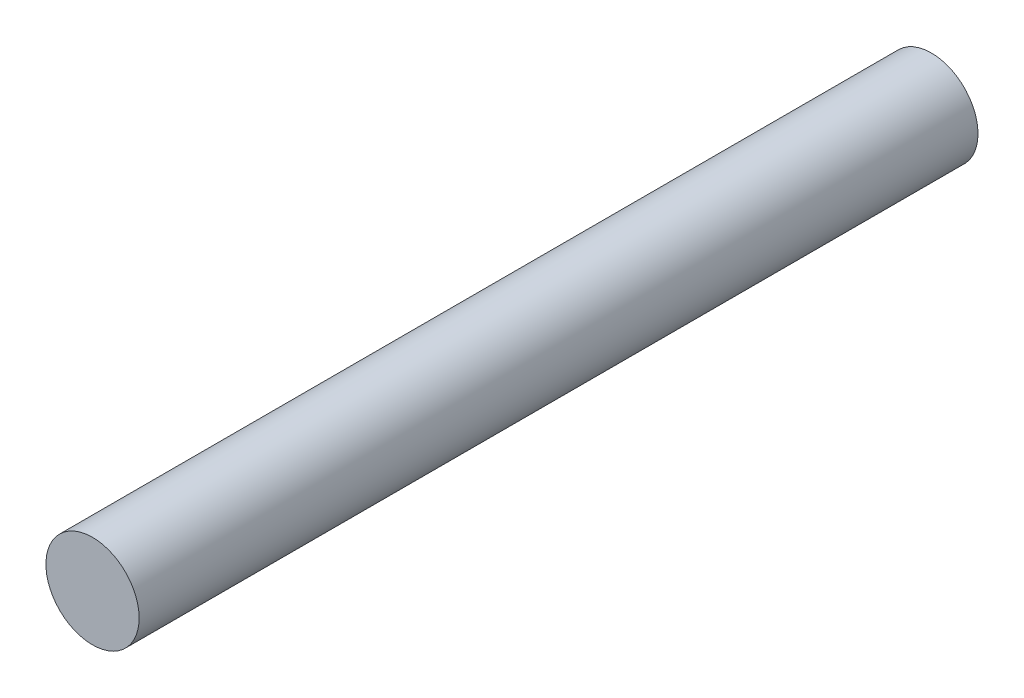
SolidWorks part; units mm, degrees
ref_plane "Front Plane" through (0, 0, 0) normal (0, 0, 1) x (1, 0, 0)
ref_plane "Top Plane" through (0, 0, 0) normal (0, 1, 0) x (1, 0, 0)
ref_plane "Right Plane" through (0, 0, 0) normal (1, 0, 0) x (0, 0, -1)
sketch "Sketch1" plane through (0, 0, 0) normal (0, 0, 1) x (1, 0, 0)
  circle A0 centre (0, 0) radius 1
  dimension "D1" = 2
extrude "Boss-Extrude1" add sketch "Sketch1" along normal blind 18
ref_plane "Plane1" through (0, 0, 9) normal (0, 0, 1) x (1, 0, 0)
